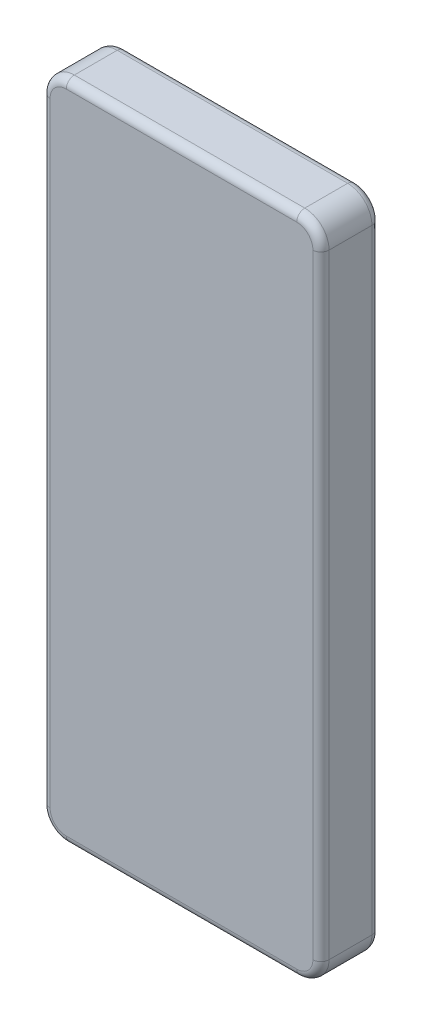
SolidWorks part; units mm, degrees
ref_plane "前视基准面" through (0, 0, 0) normal (0, 0, 1) x (1, 0, 0)
ref_plane "上视基准面" through (0, 0, 0) normal (0, 1, 0) x (1, 0, 0)
ref_plane "右视基准面" through (0, 0, 0) normal (1, 0, 0) x (0, 0, -1)
other "Configuration Table"
sketch "草图1" plane through (0, 0, 0) normal (0, 0, 1) x (1, 0, 0)
  line L1 (-14.25, 41) -> (14.25, 41)
  line L2 (-17.25, 38) -> (-17.25, -38)
  line L3 (-14.25, -41) -> (14.25, -41)
  line L4 (17.25, 38) -> (17.25, -38)
  line L5 (-17.25, 41) -> (17.25, -41) construction
  line L6 (-17.25, -41) -> (17.25, 41) construction
  arc A0 (-14.25, -41) -> (-17.25, -38) centre (-14.25, -38) cw
  arc A1 (14.25, -41) -> (17.25, -38) centre (14.25, -38) ccw
  arc A2 (17.25, 38) -> (14.25, 41) centre (14.25, 38) ccw
  arc A3 (-14.25, 41) -> (-17.25, 38) centre (-14.25, 38) ccw
  point P0 (0, 0)
  dimension "D3" = 3
  dimension "D1" = 34.5
  dimension "D2" = 82
extrude "凸台-拉伸1" add sketch "草图1" along normal blind 7.3
fillet "圆角1" radius 1 16 edges at (0, -41, 0) (16.3713, -40.1213, 0) (17.25, 0, 0) (16.3713, 40.1213, 0) (0, 41, 0) (-16.3713, 40.1213, 0) (-17.25, 0, 0) (-16.3713, -40.1213, 0) (-17.25, 0, 7.3) (-16.3713, 40.1213, 7.3) (0, 41, 7.3) (16.3713, 40.1213, 7.3) (17.25, 0, 7.3) (16.3713, -40.1213, 7.3) (0, -41, 7.3) (-16.3713, -40.1213, 7.3)
